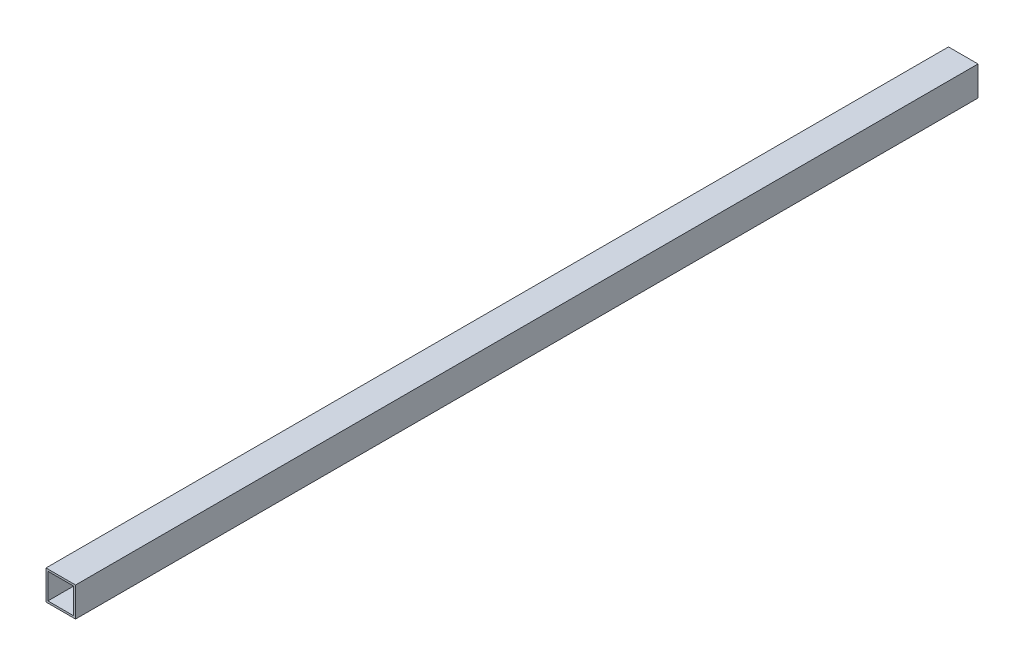
SolidWorks part; units mm, degrees
ref_plane "Front Plane" through (0, 0, 0) normal (0, 0, 1) x (1, 0, 0)
ref_plane "Top Plane" through (0, 0, 0) normal (0, 1, 0) x (1, 0, 0)
ref_plane "Right Plane" through (0, 0, 0) normal (1, 0, 0) x (0, 0, -1)
sketch "Sketch3" plane through (0, 0, 0) normal (0, 1, 0) x (1, 0, 0)
  line L0 (0, 0) -> (0, 776)
  dimension "D1" = 776
other "Al tube square AL TUBE 1 SQR X 0.065 WALL(1)"
ref_plane "Plane1" through (0, 0, 0) normal (0, 0, -1) x (-1, 0, 0)
sketch "Sketch1" plane through (0, 0, 0) normal (0, 0, -1) x (-1, 0, 0)
  line L0 (-11.049, -11.049) -> (-11.049, 11.049)
  line L1 (11.049, 11.049) -> (-11.049, 11.049)
  line L2 (11.049, 11.049) -> (11.049, -11.049)
  line L3 (-11.049, -11.049) -> (11.049, -11.049)
  line L4 (-12.7, -12.7) -> (12.7, -12.7)
  line L5 (-12.7, -12.7) -> (-12.7, 12.7)
  line L6 (12.7, 12.7) -> (-12.7, 12.7)
  line L7 (12.7, 12.7) -> (12.7, -12.7)
  line L8 (0, -11.049) -> (0, -12.7) construction
  line L9 (0, -11.049) -> (0, 11.049) construction
  line L10 (0, 11.049) -> (0, 12.7) construction
  line L11 (12.7, 0) -> (11.049, 0) construction
  line L12 (11.049, 0) -> (-11.049, 0) construction
  line L13 (-11.049, 0) -> (-12.7, 0) construction
  point P14 (0, 0)
  point P17 (0, 0)
  dimension "Thickness" = 1.651
  dimension "V_leg" = 25.4
  dimension "H_leg" = 25.4
